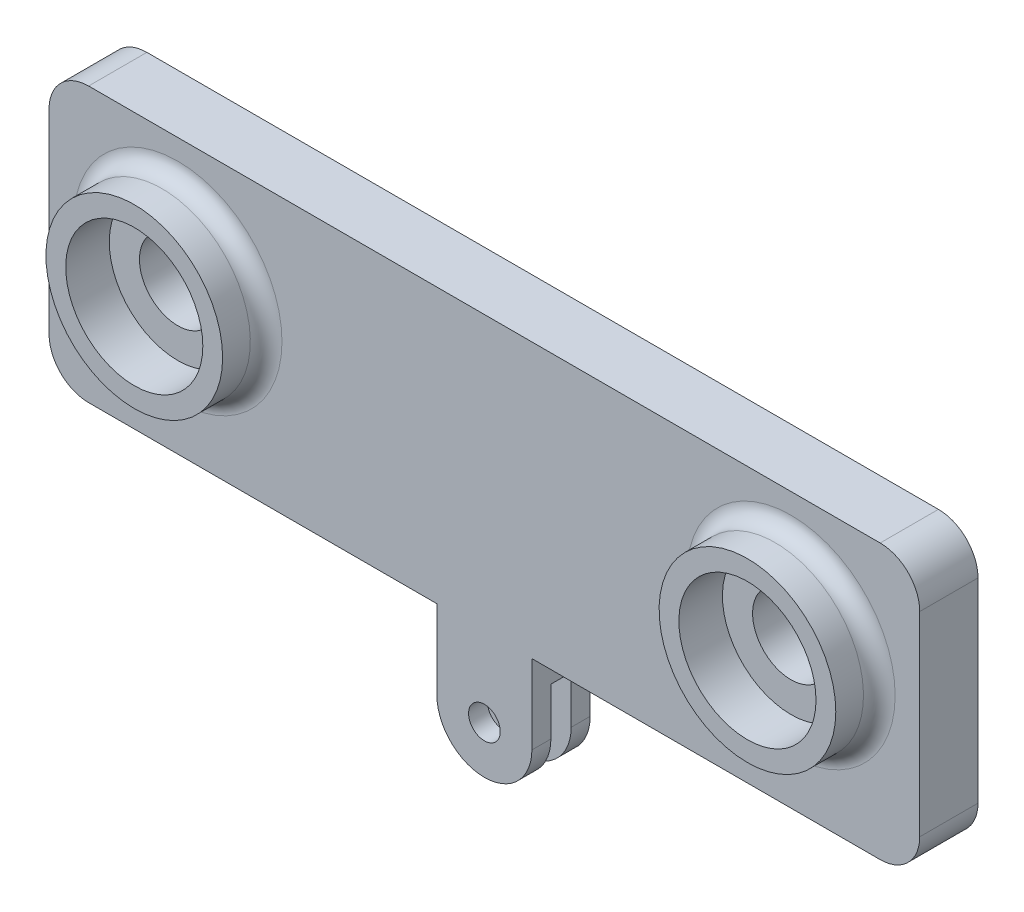
SolidWorks part; units mm, degrees
material "ABS"
ref_plane "Front Plane" through (0, 0, 0) normal (0, 0, 1) x (1, 0, 0)
ref_plane "Top Plane" through (0, 0, 0) normal (0, 1, 0) x (1, 0, 0)
ref_plane "Right Plane" through (0, 0, 0) normal (1, 0, 0) x (0, 0, -1)
sketch "Sketch1" plane through (0, 0, 0) normal (1, 0, 0) x (0, 0, -1)
  line L0 (-4.6736, 0) -> (-4.6736, 5.08)
  line L1 (-4.6736, 5.08) -> (4.6736, 5.08)
  line L2 (4.6736, 5.08) -> (4.6736, 0)
  line L3 (0, 0) -> (0, -15.24) construction
  line L4 (-1.6256, 0) -> (-1.6256, -15.24)
  line L5 (1.6256, 0) -> (1.6256, -15.24)
  line L6 (-4.6736, 0) -> (-4.6736, -15.24)
  line L7 (4.6736, 0) -> (4.6736, -15.24)
  line L8 (-4.6736, -15.24) -> (-1.6256, -15.24)
  line L9 (1.6256, -15.24) -> (4.6736, -15.24)
  line L10 (-1.6256, 0) -> (1.6256, 0)
  dimension "D2" = 5.08
  dimension "D8" = 3.048
  dimension "D9" = 3.048
  dimension "D10" = 15.24
  dimension "D6" = 1.6256
  dimension "D7" = 1.6256
extrude "Boss-Extrude1" add sketch "Sketch1" against normal blind 15.24
sketch "Sketch2" plane through (0, 0, 4.6736) normal (0, 0, 1) x (1, 0, 0)
  line L0 (-7.62, 0) -> (-7.62, -15.24) construction
  line L2 (-15.24, -15.24) -> (0, -15.24) construction
  line L3 (0, 5.08) -> (0, -15.24) construction
  line L4 (-15.24, -7.62) -> (-15.24, 0)
  line L5 (-15.24, 0) -> (0, 0)
  line L6 (0, 0) -> (0, -7.62)
  circle A0 centre (-7.62, -7.62) radius 2.54
  arc A1 (-15.24, -7.62) -> (0, -7.62) centre (-7.62, -7.62) ccw
  line M1 (0, -15.24) -> (0, 5.08)
  line M3 (-15.24, 5.08) -> (-15.24, -15.24)
  line M4 (-15.24, -15.24) -> (0, -15.24)
  dimension "D1" = 5.08
extrude "Cut-Extrude1" cut sketch "Sketch2" against normal through all contours L0 A0 | A0 L0 | A1 M3 M4 | A1 M4 M1
sketch "Sketch3" plane through (0, 0, 4.6736) normal (0, 0, 1) x (1, 0, 0)
  line L0 (-15.24, 5.08) -> (0, 5.08) construction
  line L1 (-77.47, 5.08) -> (62.23, 5.08)
  line L2 (-77.47, 5.08) -> (-77.47, 49.08)
  line L3 (-77.47, 49.08) -> (62.23, 49.08)
  line L4 (62.23, 5.08) -> (62.23, 49.08)
  line L6 (-15.24, 5.08) -> (0, 5.08) construction
  point P6 (-7.62, 5.08)
  point P9 (-7.62, 5.08)
  dimension "D1" = 139.7
  dimension "D3" = 44
extrude "Boss-Extrude2" add sketch "Sketch3" against normal up to surface (9.3472 mm away) up to face at (-5.08, -7.62, -4.6736)
fillet "Fillet1" radius 6.35 4 edges at (-77.47, 5.08, 0) (-77.47, 49.08, 0) (62.23, 5.08, 0) (62.23, 49.08, 0)
sketch "Sketch6" plane through (0, 0, 4.6736) normal (0, 0, 1) x (1, 0, 0)
  line L0 (-77.47, 42.73) -> (-77.47, 11.43) construction
  line L2 (55.88, 49.08) -> (-71.12, 49.08) construction
  circle A0 centre (-56.81, 29.08) radius 6.1595
  circle A1 centre (41.57, 29.08) radius 6.1595
  dimension "D4" = 20
  dimension "D1" = 12.319
  dimension "D2" = 20.66
  dimension "D3" = 119.04
extrude "Cut-Extrude2" cut sketch "Sketch6" against normal through all
sketch "Sketch7" plane through (0, 0, -4.6736) normal (0, 0, -1) x (-1, 0, 0)
  line L0 (77.47, 42.73) -> (77.47, 11.43) construction
  line L1 (-55.88, 49.08) -> (71.12, 49.08) construction
  line L2 (77.47, 42.73) -> (77.47, 11.43) construction
  line L3 (-55.88, 49.08) -> (71.12, 49.08) construction
  circle A0 centre (30.48, 35.97) radius 0.9652
  circle A1 centre (-15.24, 35.97) radius 0.9652
  circle A2 centre (30.48, 18.19) radius 0.9652
  circle A3 centre (-15.24, 18.19) radius 0.9652
  circle A6 centre (7.62, 7.649) radius 0.9652
  circle A7 centre (7.62, 46.511) radius 0.9652
  dimension "D1" = 1.9304
  dimension "D2" = 46.99
  dimension "D3" = 92.71
  dimension "D4" = 13.11
  dimension "D5" = 30.89
  dimension "D6" = 69.85
  dimension "D7" = 2.569
  dimension "D8" = 41.431
extrude "Cut-Extrude3" cut sketch "Sketch7" against normal blind 5.588
sketch "Sketch8" plane through (0, 0, -4.6736) normal (0, 0, -1) x (-1, 0, 0)
  line L1 (77.47, 42.73) -> (77.47, 11.43) construction
  line L2 (-55.88, 49.08) -> (71.12, 49.08) construction
  circle A0 centre (-41.57, 37.83) radius 0.8065
  circle A1 centre (-41.57, 9.83) radius 0.8065
  circle A2 centre (56.81, 37.83) radius 0.8064
  circle A3 centre (56.81, 9.83) radius 0.8064
  dimension "D1" = 1.6129
  dimension "D2" = 20.66
  dimension "D3" = 119.04
  dimension "D4" = 11.25
  dimension "D5" = 39.25
extrude "Cut-Extrude4" cut sketch "Sketch8" against normal blind 5.08
sketch "Sketch9" plane through (0, 0, 4.6736) normal (0, 0, 1) x (1, 0, 0)
  line L0 (-77.47, 42.73) -> (-77.47, 11.43) construction
  line L1 (55.88, 49.08) -> (-71.12, 49.08) construction
  circle A0 centre (-56.81, 29.08) radius 11
  circle A1 centre (41.57, 29.08) radius 11
  circle A2 centre (-56.81, 29.08) radius 14.175
  circle A3 centre (41.57, 29.08) radius 14.175
  dimension "D1" = 22
  dimension "D2" = 28.35
  dimension "D3" = 20.66
  dimension "D4" = 119.04
  dimension "D5" = 20
extrude "Boss-Extrude5" add sketch "Sketch9" along normal blind 6.985
fillet "Fillet2" radius 2.54 2 edges at (-42.635, 29.08, 4.6736) (55.745, 29.08, 4.6736)
